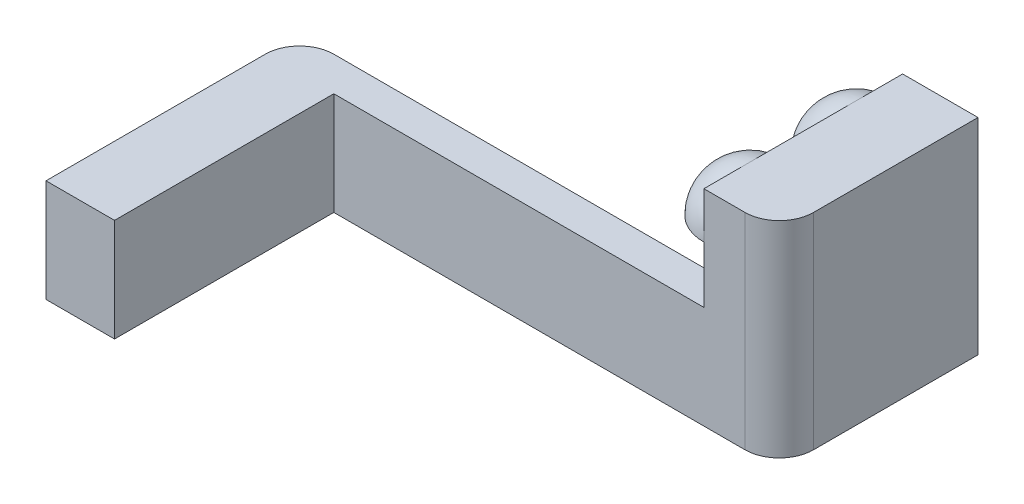
SolidWorks part; units mm, degrees
ref_plane "Front Plane" through (0, 0, 0) normal (0, 0, 1) x (1, 0, 0)
ref_plane "Top Plane" through (0, 0, 0) normal (0, 1, 0) x (1, 0, 0)
ref_plane "Right Plane" through (0, 0, 0) normal (1, 0, 0) x (0, 0, -1)
other "Configuration Table"
sketch "Sketch1" plane through (0, 0, 0) normal (0, 0, 1) x (1, 0, 0)
  line L1 (30, 7.5) -> (-30, 7.5)
  line L2 (30, 7.5) -> (30, -7.5)
  line L3 (30, -7.5) -> (-30, -7.5)
  line L4 (-30, 7.5) -> (-30, -7.5)
  line L5 (30, 7.5) -> (-30, -7.5) construction
  line L6 (30, -7.5) -> (-30, 7.5) construction
  point P0 (0, 0)
  dimension "D1" = 60
  dimension "D2" = 15
extrude "Boss-Extrude1" add sketch "Sketch1" along normal blind 5
sketch "Sketch2" plane through (-30, 0, 0) normal (-1, 0, 0) x (0, 0, 1)
  line L0 (5, -7.5) -> (0, -7.5) construction
  line L1 (5, 7.5) -> (-32, 7.5)
  line L2 (5, 7.5) -> (5, -7.5)
  line L3 (5, -7.5) -> (-32, -7.5)
  line L4 (-32, 7.5) -> (-32, -7.5)
  dimension "D1" = 37
extrude "Boss-Extrude2" add sketch "Sketch2" along normal blind 10
fillet "Fillet1" radius 5 1 edges at (-40, 0, 5)
sketch "Sketch3" plane through (30, 0, 0) normal (1, 0, 0) x (0, 0, -1)
  line L1 (0, 22.5) -> (-29, 22.5)
  line L2 (0, 22.5) -> (0, -7.5)
  line L3 (0, -7.5) -> (-29, -7.5)
  line L4 (-29, 22.5) -> (-29, -7.5)
  line L5 (-5, -7.5) -> (0, -7.5) construction
  line L6 (0, 13.6459) -> (0, -13.6459) construction
  dimension "D1" = 29
  dimension "D2" = 30
extrude "Boss-Extrude3" add sketch "Sketch3" along normal blind 5
fillet "Fillet2" radius 5 1 edges at (35, 7.5, 0)
sketch "Sketch8" plane through (0, 0, 5) normal (0, 0, 1) x (1, 0, 0)
  line L1 (35, 22.5) -> (30, 22.5) construction
  line L12 (30, -7.5) -> (30, 7.5) construction
  line L13 (30, 22.5) -> (24, 22.5)
  line L14 (30, 22.5) -> (30, -7.5)
  line L15 (30, -7.5) -> (24, -7.5)
  line L16 (24, 22.5) -> (24, -7.5)
  line L18 (-35, -7.5) -> (30, -7.5) construction
  line L19 (30, 22.5) -> (30, -7.5) construction
  dimension "D1" = 6
extrude "Boss-Extrude6" add sketch "Sketch8" along normal up to surface and the other way up to surface up to face at (32.5, 7.5, 29) other way up to face at (0, 0, 0)
sketch "Sketch7" plane through (0, -7.5, 0) normal (0, -1, 0) x (1, 0, 0)
  line L0 (35, 29) -> (35, 5) construction
  line L1 (33, 27) -> (27, 27)
  line L2 (33, 27) -> (33, 5)
  line L3 (33, 5) -> (27, 5)
  line L4 (27, 27) -> (27, 5)
  line L5 (33, 27) -> (27, 5) construction
  line L6 (33, 5) -> (27, 27) construction
  line L7 (13.6459, 0) -> (-13.6459, 0) construction
  line L8 (-40, -32) -> (-40, 0) construction
  line L9 (-32, -5) -> (-38, -5)
  line L10 (-32, -5) -> (-32, -27)
  line L11 (-32, -27) -> (-38, -27)
  line L12 (-38, -5) -> (-38, -27)
  line L13 (-32, -5) -> (-38, -27) construction
  line L14 (-32, -27) -> (-38, -5) construction
  line L15 (-40, -32) -> (-30, -32) construction
  point P0 (30, 16)
  point P9 (-35, -16)
  dimension "D1" = 22
  dimension "D2" = 6
  dimension "D3" = 2
  dimension "D4" = 5
  dimension "D5" = 2
  dimension "D6" = 5
extrude "Cut-Extrude3" cut sketch "Sketch7" against normal blind 11
sketch "Sketch9" plane through (24, 0, 0) normal (-1, 0, 0) x (0, 0, 1)
  line L0 (29, -7.5) -> (29, 22.5) construction
  line L1 (0, 22.5) -> (0, 7.5) construction
  line L2 (29, 22.5) -> (0, 22.5) construction
  line L3 (0, 15.75) -> (13.5, 15.75)
  line L4 (15.5, 15.75) -> (29, 15.75)
  arc A0 (13.5, 15.75) -> (0, 15.75) centre (6.75, 15.75) ccw
  arc A1 (29, 15.75) -> (15.5, 15.75) centre (22.25, 15.75) ccw
  dimension "D1" = 13.5
revolve "Revolve1" add sketch "Sketch9" angle 90 about L3
mirror "Mirror1" about plane through (-40, 7.5, -32) normal (0, 0, 1) of bodies 116
delete or keep bodies "Body-Delete/Keep 1" type delete bodies bodies 116
